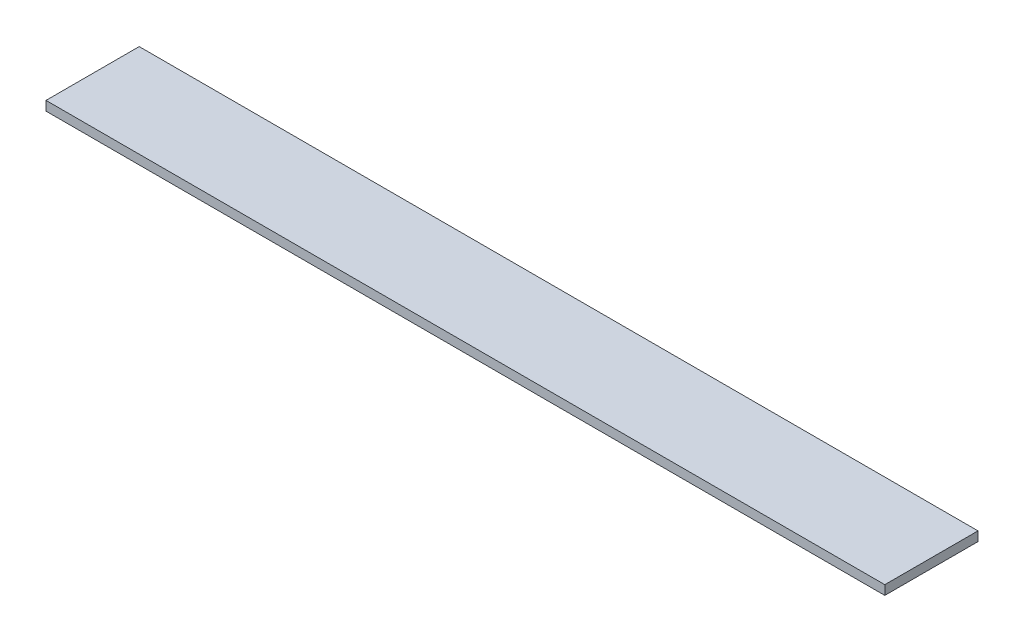
SolidWorks part; units mm, degrees
ref_plane "Face" through (0, 0, 0) normal (0, 0, 1) x (1, 0, 0)
ref_plane "Dessus" through (0, 0, 0) normal (0, 1, 0) x (1, 0, 0)
ref_plane "Droite" through (0, 0, 0) normal (1, 0, 0) x (0, 0, -1)
sketch "Esquisse1" plane through (0, 0, 0) normal (0, 1, 0) x (1, 0, 0)
  line L1 (0, 0) -> (900, 0)
  line L2 (0, 0) -> (0, 100)
  line L3 (0, 100) -> (900, 100)
  line L4 (900, 0) -> (900, 100)
  dimension "D1" = 900
  dimension "D2" = 100
extrude "Extrusion1" add sketch "Esquisse1" along normal blind 10
